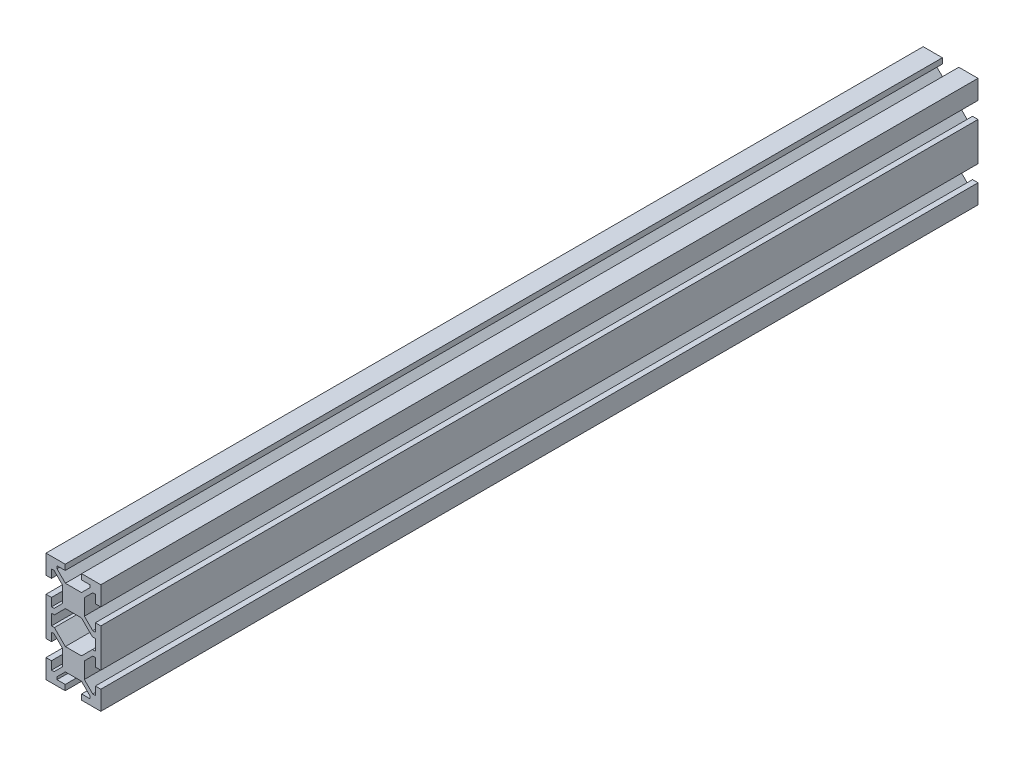
SolidWorks part; units mm, degrees
ref_plane "Front Plane" through (0, 0, 0) normal (0, 0, 1) x (1, 0, 0)
ref_plane "Top Plane" through (0, 0, 0) normal (0, 1, 0) x (1, 0, 0)
ref_plane "Right Plane" through (0, 0, 0) normal (1, 0, 0) x (0, 0, -1)
sketch "Sketch1" plane through (0, 0, 0) normal (0, 0, 1) x (1, 0, 0)
  line L0 (-6, -17.0607) -> (-2.9393, -14)
  line L1 (-2.9393, -14) -> (2.9393, -14)
  line L2 (2.9393, -14) -> (6, -17.0607)
  line L3 (6, -17.0607) -> (6, -18)
  line L4 (6, -18) -> (3, -18)
  line L5 (3, -18) -> (3, -20)
  line L6 (3, -20) -> (10, -20)
  line L7 (10, -20) -> (10, -13)
  line L8 (10, -13) -> (8, -13)
  line L9 (8, -13) -> (8, -16)
  line L10 (8, -16) -> (7.0607, -16)
  line L11 (7.0607, -16) -> (4, -12.9393)
  line L12 (4, -12.9393) -> (4, -7.0607)
  line L13 (4, -7.0607) -> (7.0607, -4)
  line L14 (7.0607, -4) -> (8, -4)
  line L15 (8, -4) -> (8, -7)
  line L16 (8, -7) -> (10, -7)
  line L17 (10, -7) -> (10, 7)
  line L18 (10, 7) -> (8, 7)
  line L19 (8, 7) -> (8, 4)
  line L20 (8, 4) -> (7.0607, 4)
  line L21 (7.0607, 4) -> (4, 7.0607)
  line L22 (4, 7.0607) -> (4, 12.9393)
  line L23 (4, 12.9393) -> (7.0607, 16)
  line L24 (7.0607, 16) -> (8, 16)
  line L25 (8, 16) -> (8, 13)
  line L26 (8, 13) -> (10, 13)
  line L27 (10, 13) -> (10, 20)
  line L28 (10, 20) -> (3, 20)
  line L29 (3, 20) -> (3, 18)
  line L30 (3, 18) -> (6, 18)
  line L31 (6, 18) -> (6, 17.0607)
  line L32 (6, 17.0607) -> (2.9393, 14)
  line L33 (2.9393, 14) -> (-2.9393, 14)
  line L34 (-2.9393, 14) -> (-6, 17.0607)
  line L35 (-6, 17.0607) -> (-6, 18)
  line L36 (-6, 18) -> (-3, 18)
  line L37 (-3, 18) -> (-3, 20)
  line L38 (-3, 20) -> (-10, 20)
  line L39 (-10, 20) -> (-10, 13)
  line L40 (-10, 13) -> (-8, 13)
  line L41 (-8, 13) -> (-8, 16)
  line L42 (-8, 16) -> (-7.0607, 16)
  line L43 (-7.0607, 16) -> (-4, 12.9393)
  line L44 (-4, 12.9393) -> (-4, 7.0607)
  line L45 (-4, 7.0607) -> (-7.0607, 4)
  line L46 (-7.0607, 4) -> (-8, 4)
  line L47 (-8, 4) -> (-8, 7)
  line L48 (-8, 7) -> (-10, 7)
  line L49 (-10, 7) -> (-10, -7)
  line L50 (-10, -7) -> (-8, -7)
  line L51 (-8, -7) -> (-8, -4)
  line L52 (-8, -4) -> (-7.0607, -4)
  line L53 (-7.0607, -4) -> (-4, -7.0607)
  line L54 (-4, -7.0607) -> (-4, -12.9393)
  line L55 (-4, -12.9393) -> (-7.0607, -16)
  line L56 (-7.0607, -16) -> (-8, -16)
  line L57 (-8, -16) -> (-8, -13)
  line L58 (-8, -13) -> (-10, -13)
  line L59 (-10, -13) -> (-10, -20)
  line L60 (-10, -20) -> (-3, -20)
  line L61 (-3, -20) -> (-3, -18)
  line L62 (-3, -18) -> (-6, -18)
  line L63 (-6, -18) -> (-6, -17.0607)
  line L64 (-6.9393, -2) -> (-8, -2)
  line L65 (-8, -2) -> (-8, 2)
  line L66 (-8, 2) -> (-6.9393, 2)
  line L67 (-6.9393, 2) -> (-2.9393, 6)
  line L68 (-2.9393, 6) -> (2.9393, 6)
  line L69 (2.9393, 6) -> (6.9393, 2)
  line L70 (6.9393, 2) -> (8, 2)
  line L71 (8, 2) -> (8, -2)
  line L72 (8, -2) -> (6.9393, -2)
  line L73 (6.9393, -2) -> (2.9393, -6)
  line L74 (2.9393, -6) -> (-2.9393, -6)
  line L75 (-2.9393, -6) -> (-6.9393, -2)
extrude "Boss-Extrude1" add sketch "Sketch1" against normal mid plane 320
hole_wizard "Ø4.2 (4.2) Diameter Hole1" [suppressed] positions "Sketch3" profile "Sketch2" hole size "Ø4.2" standard "ANSI Metric"
sketch "Sketch3" plane through (0, 0, -320) normal (0, 0, -1) x (-1, 0, 0)
  point P0 (0, 10)
sketch "Sketch2" plane through (0, 10, -320) normal (1, 0, 0) x (0, 1, 0)
  line L0 (0, 0) -> (0, 320)
  line L1 (0, 320) -> (2.1, 320)
  line L2 (2.1, 320) -> (2.1, 0)
  line L5 (2.1, 0) -> (0, 0)
  line L11 (0, -6.35) -> (0, 107.95) construction
  dimension "Thru Hole Dia." = 4.2
  dimension "Thru Hole Depth" = 320
hole_wizard "Ø4.2 (4.2) Diameter Hole2" [suppressed] positions "Sketch5" profile "Sketch4" hole size "Ø4.2" standard "ANSI Metric"
sketch "Sketch5" plane through (0, 0, -320) normal (0, 0, -1) x (-1, 0, 0)
  point P0 (0, -10)
sketch "Sketch4" plane through (0, -10, -320) normal (1, 0, 0) x (0, 1, 0)
  line L0 (0, 0) -> (0, 320)
  line L1 (0, 320) -> (2.1, 320)
  line L2 (2.1, 320) -> (2.1, 0)
  line L5 (2.1, 0) -> (0, 0)
  line L11 (0, -6.35) -> (0, 107.95) construction
  dimension "Thru Hole Dia." = 4.2
  dimension "Thru Hole Depth" = 320
fillet "Fillet1" [suppressed] radius 0.3
fillet "Fillet2" [suppressed] radius 0.3
fillet "Fillet3" [suppressed] radius 1
